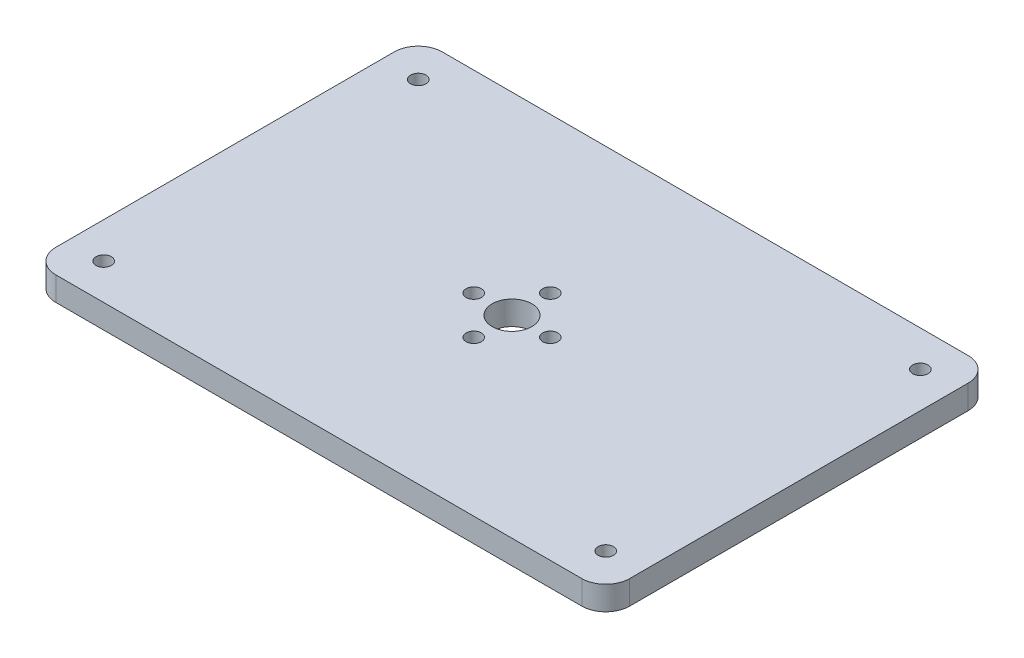
SolidWorks part; units mm, degrees
material "Acrylic (Medium-high impact)"
ref_plane "Front Plane" through (0, 0, 0) normal (0, 0, 1) x (1, 0, 0)
ref_plane "Top Plane" through (0, 0, 0) normal (0, 1, 0) x (1, 0, 0)
ref_plane "Right Plane" through (0, 0, 0) normal (1, 0, 0) x (0, 0, -1)
sketch "Sketch1" plane through (0, 0, 0) normal (0, 1, 0) x (1, 0, 0)
  line L0 (60, 80.79) -> (60, 0) construction
  line L1 (0, 0) -> (120, 0)
  line L2 (0, 0) -> (0, 80.79)
  line L3 (0, 80.79) -> (120, 80.79)
  line L4 (120, 0) -> (120, 80.79)
  line L5 (0, 40.395) -> (120, 40.395) construction
  circle A0 centre (52, 40.395) radius 1.6
  circle A1 centre (60, 48.395) radius 1.6
  circle A2 centre (68, 40.395) radius 1.6
  circle A3 centre (60, 32.395) radius 1.6
  circle A4 centre (60, 40.395) radius 4.15
  point P11 (60, 40.395)
  dimension "D3" = 3.2
  dimension "D4" = 8
  dimension "D6" = 8.3
  dimension "D1" = 120
  dimension "D2" = 80.79
  dimension "D5" = 4
extrude "Boss-Extrude1" add sketch "Sketch1" along normal blind 5
sketch "Sketch2" plane through (0, 5, 0) normal (0, 1, 0) x (1, 0, 0)
  line L0 (7.5, 80.79) -> (7.5, 0) construction
  line L1 (120, 80.79) -> (0, 80.79) construction
  line L2 (0, 0) -> (120, 0) construction
  line L3 (60, 80.79) -> (60, 0) construction
  line L4 (0, 40.395) -> (120, 40.395) construction
  line L5 (0, 80.79) -> (0, 0) construction
  line L6 (120, 0) -> (120, 80.79) construction
  circle A0 centre (7.5, 7.5) radius 1.6
  circle A1 centre (7.5, 73.29) radius 1.6
  circle A2 centre (112.5, 7.5) radius 1.6
  circle A3 centre (112.5, 73.29) radius 1.6
  dimension "D1" = 7.5
  dimension "D2" = 3.2
  dimension "D3" = 7.5
extrude "Cut-Extrude1" cut sketch "Sketch2" against normal through all
fillet "Fillet1" radius 5 4 edges at (120, 2.5, -80.79) (120, 2.5, 0) (0, 2.5, 0) (0, 2.5, -80.79)
